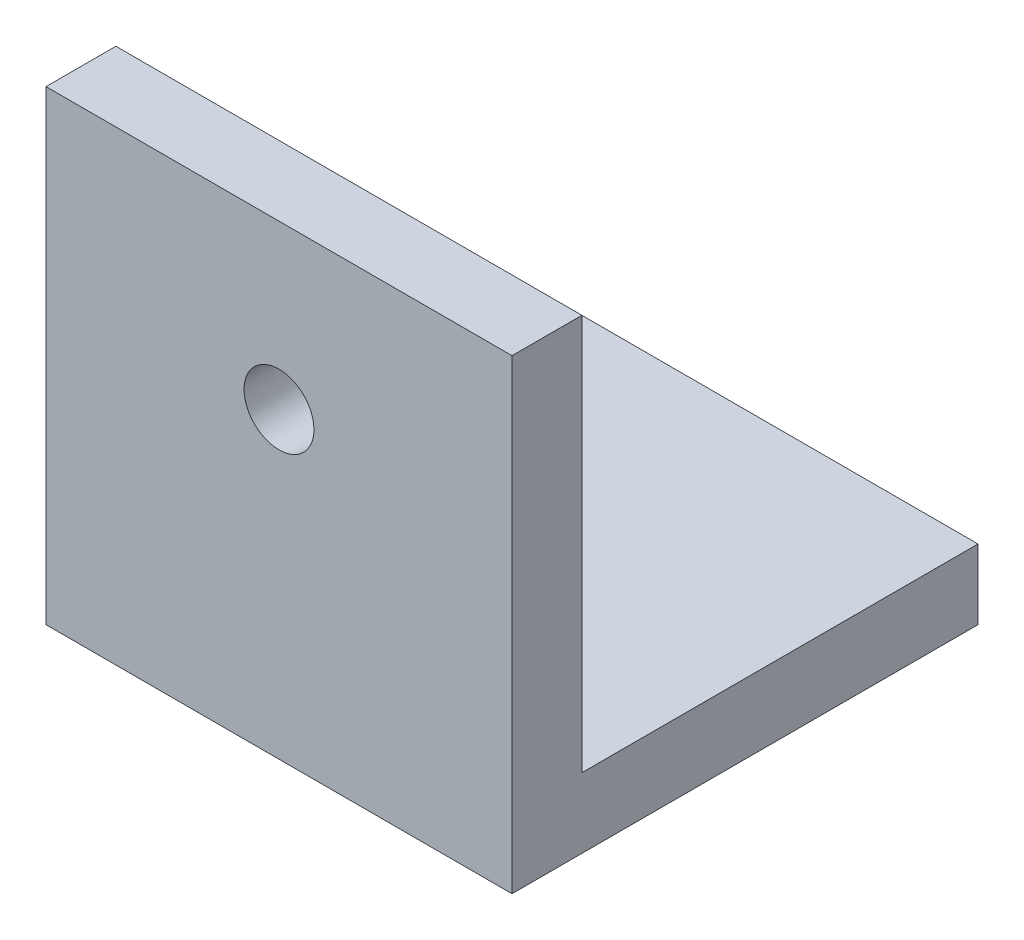
SolidWorks part; units mm, degrees
ref_plane "Front Plane" through (0, 0, 0) normal (0, 0, 1) x (1, 0, 0)
ref_plane "Top Plane" through (0, 0, 0) normal (0, 1, 0) x (1, 0, 0)
ref_plane "Right Plane" through (0, 0, 0) normal (1, 0, 0) x (0, 0, -1)
sketch "Sketch1" plane through (0, 0, 0) normal (0, 0, 1) x (1, 0, 0)
  line L0 (-58.1522, 0) -> (51.9928, 0) construction
  line L1 (0, 59.5109) -> (0, -62.4094) construction
  line L3 (50, 50) -> (-50, 50)
  line L4 (50, 50) -> (50, -50)
  line L5 (50, -50) -> (-50, -50)
  line L6 (-50, 50) -> (-50, -50)
  circle A0 centre (0, 15) radius 7.5
  point P11 (0, 59.5109)
  point P12 (0, -62.4094)
  dimension "D2" = 15
  dimension "D4" = 35
  dimension "D1" = 100
  dimension "D3" = 100
extrude "Boss-Extrude1" add sketch "Sketch1" along normal blind 15
sketch "Sketch2" plane through (50, 0, 0) normal (1, 0, 0) x (0, 0, -1)
  line L0 (0, -35) -> (85, -35)
  line L1 (0, -50) -> (0, 50) construction
  line L2 (85, -35) -> (85, -50)
  line L3 (85, -50) -> (0, -50)
  line L4 (-15, -50) -> (-15, 50) construction
  line L5 (0, -35) -> (0, -50)
  line L6 (-15, 15) -> (0, 15) construction
  dimension "D1" = 15
  dimension "D2" = 100
  dimension "D3" = 50
  dimension "D4" = 90
extrude "Boss-Extrude2" add sketch "Sketch2" against normal blind 100
